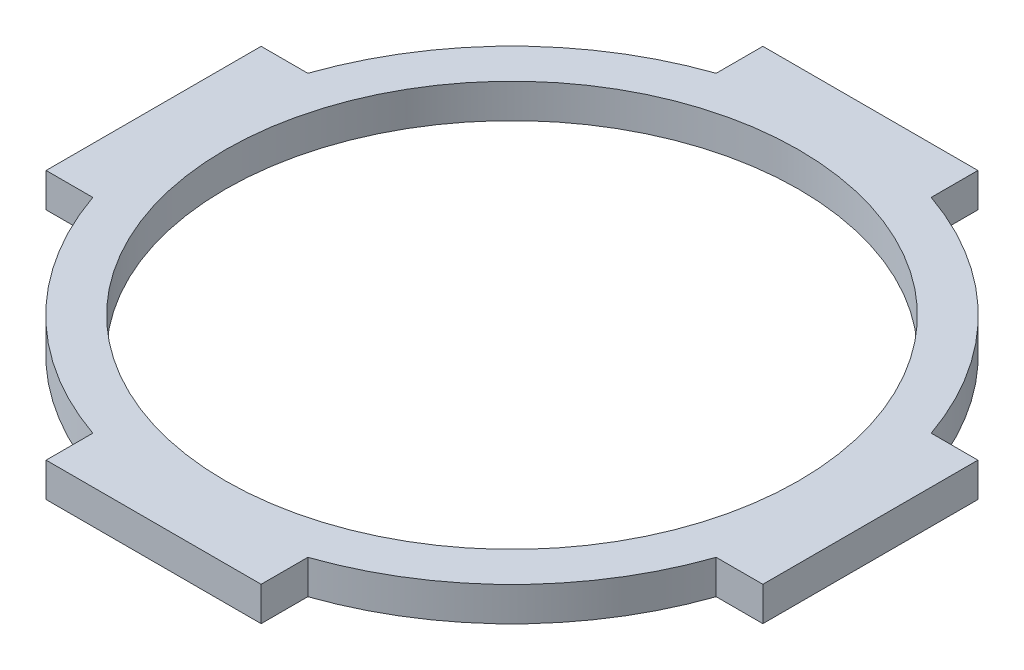
SolidWorks part; units mm, degrees
ref_plane "Front Plane" through (0, 0, 0) normal (0, 0, 1) x (1, 0, 0)
ref_plane "Top Plane" through (0, 0, 0) normal (0, 1, 0) x (1, 0, 0)
ref_plane "Right Plane" through (0, 0, 0) normal (1, 0, 0) x (0, 0, -1)
sketch "Sketch1" plane through (0, 0, 0) normal (0, 1, 0) x (1, 0, 0)
  circle A0 centre (0, 0) radius 46
  circle A1 centre (0, 0) radius 40
  dimension "D1" = 6
  dimension "D2" = 80
extrude "Boss-Extrude1" add sketch "Sketch1" along normal blind 4.7625
sketch "Sketch2" plane through (0, 4.7625, 0) normal (0, 1, 0) x (1, 0, 0)
  line L0 (-43.4856, 15) -> (-50, 15)
  line L1 (-50, 15) -> (-50, -15)
  line L2 (-50, -15) -> (-43.4856, -15)
  circle A0 centre (0, 0) radius 46 construction
  arc A1 (-43.4856, 15) -> (-43.4856, -15) centre (0, 0) ccw
  dimension "D1" = 50
  dimension "D2" = 30
extrude "Boss-Extrude2" add sketch "Sketch2" against normal up to surface (4.7625 mm away) up to face at (0, 0, 46)
pattern_circular "CirPattern1" count 4 over 360 about axis through (0, 0, 0) along (0, 1, 0) of "Boss-Extrude2"
sketch "Sketch3" plane through (0, 4.7625, 0) normal (0, 1, 0) x (1, 0, 0)
  line L12 (-15, -43.4856) -> (-15, -50)
  line L13 (-15, -50) -> (15, -50)
  line L14 (15, -50) -> (15, -43.4856)
  line L15 (43.4856, -15) -> (50, -15)
  line L16 (50, -15) -> (50, 15)
  line L17 (50, 15) -> (43.4856, 15)
  line L18 (15, 43.4856) -> (15, 50)
  line L19 (15, 50) -> (-15, 50)
  line L20 (-15, 50) -> (-15, 43.4856)
  line L21 (-43.4856, 15) -> (-50, 15)
  line L22 (-50, 15) -> (-50, -15)
  line L23 (-50, -15) -> (-43.4856, -15)
  line L24 (-15, -43.4856) -> (-15, -50)
  line L25 (-15, -50) -> (15, -50)
  line L26 (15, -50) -> (15, -43.4856)
  line L27 (43.4856, -15) -> (50, -15)
  line L28 (50, -15) -> (50, 15)
  line L29 (50, 15) -> (43.4856, 15)
  line L30 (15, 43.4856) -> (15, 50)
  line L31 (15, 50) -> (-15, 50)
  line L32 (-15, 50) -> (-15, 43.4856)
  line L33 (-43.4856, 15) -> (-50, 15)
  line L34 (-50, 15) -> (-50, -15)
  line L35 (-50, -15) -> (-43.4856, -15)
  circle A0 centre (0, 0) radius 40 construction
  circle A1 centre (0, 0) radius 40
  arc A4 (-43.4856, -15) -> (-15, -43.4856) centre (0, 0) ccw
  arc A5 (15, -43.4856) -> (43.4856, -15) centre (0, 0) ccw
  arc A6 (43.4856, 15) -> (15, 43.4856) centre (0, 0) ccw
  arc A7 (-15, 43.4856) -> (-43.4856, 15) centre (0, 0) ccw
  arc A8 (-43.4856, -15) -> (-15, -43.4856) centre (0, 0) ccw
  arc A9 (15, -43.4856) -> (43.4856, -15) centre (0, 0) ccw
  arc A10 (43.4856, 15) -> (15, 43.4856) centre (0, 0) ccw
  arc A11 (-15, 43.4856) -> (-43.4856, 15) centre (0, 0) ccw
  dimension "D1" = 0
